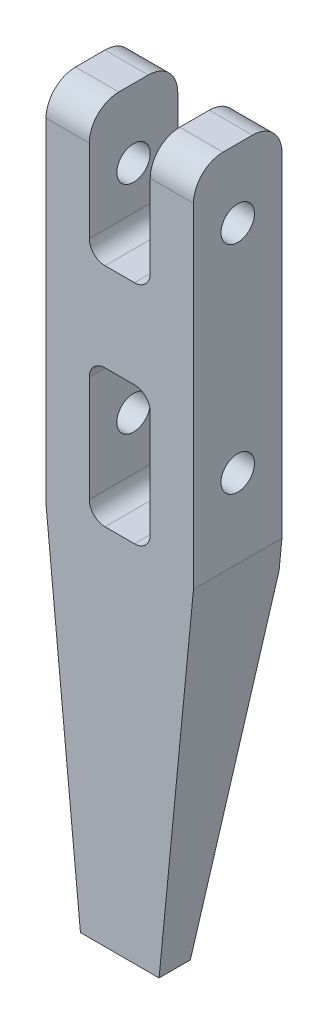
SolidWorks part; units mm, degrees
ref_plane "前视基准面" through (0, 0, 0) normal (0, 0, 1) x (1, 0, 0)
ref_plane "上视基准面" through (0, 0, 0) normal (0, 1, 0) x (1, 0, 0)
ref_plane "右视基准面" through (0, 0, 0) normal (1, 0, 0) x (0, 0, -1)
sketch "草图1" plane through (0, 0, 0) normal (1, 0, 0) x (0, 0, -1)
  line L0 (0, 0) -> (0, -11) construction
  line L1 (-2.25, 3.5) -> (2.25, 3.5)
  line L2 (2.25, 3.5) -> (2.25, -16.5)
  line L3 (2.25, -16.5) -> (-0.6594, -33)
  line L4 (-0.6594, -33) -> (-2.25, -33)
  line L5 (-2.25, -33) -> (-2.25, 3.5)
  circle A0 centre (0, 0) radius 0.85
  circle A1 centre (0, -11) radius 0.85
  dimension "D1" = 1.7
  dimension "D2" = 11
  dimension "D3" = 100
  dimension "D4" = 3.5
  dimension "D5" = 4.5
  dimension "D6" = 20
  dimension "D7" = 22
extrude "凸台-拉伸1" add sketch "草图1" along normal mid plane 7.5
sketch "草图2" plane through (0, 0, 0) normal (0, 0, 1) x (1, 0, 0)
  line L0 (3.75, -0.85) -> (3.75, 0.85) construction
  line L1 (3.75, -11.85) -> (3.75, -10.15) construction
  line L2 (3.75, -0.85) -> (3.75, 0.85)
  line L3 (3.75, -11.85) -> (3.75, -10.15)
  line L4 (0, 0) -> (0, -31.8275) construction
  line L5 (3.75, 0) -> (-9.2261, 0) construction
  line L6 (3.75, -11) -> (-10.1426, -11) construction
  line L8 (-1.55, 4.7829) -> (1.55, 4.7829)
  line L9 (-1.55, 4.7829) -> (-1.55, -3)
  line L10 (-1.55, -3) -> (1.55, -3)
  line L11 (1.55, 4.7829) -> (1.55, -3)
  line L12 (-1.55, -7.5) -> (1.55, -7.5)
  line L13 (-1.55, -7.5) -> (-1.55, -14.5)
  line L14 (-1.55, -14.5) -> (1.55, -14.5)
  line L15 (1.55, -7.5) -> (1.55, -14.5)
  dimension "D1" = 7
  dimension "D2" = 3.1
  dimension "D3" = 3
extrude "切除-拉伸1" cut sketch "草图2" against normal through all and the other way through all contours L11 L8 L9 L10 | L15 L14 L13 L12
fillet "圆角1" radius 1.5 4 edges at (2.65, 3.5, 2.25) (2.65, 3.5, -2.25) (-2.65, 3.5, -2.25) (-2.65, 3.5, 2.25)
fillet "圆角2" radius 0.8 6 edges at (1.55, -7.5, 0) (-1.55, -7.5, 0) (1.55, -14.5, 0) (-1.55, -14.5, 0) (-1.55, -3, 0) (1.55, -3, 0)
sketch "草图3" plane through (0, 0, 2.25) normal (0, 0, 1) x (1, 0, 0)
  line L0 (-3.75, -15) -> (-2, -33)
  line L1 (-3.75, 2) -> (-3.75, -33) construction
  line L2 (3.75, -33) -> (-3.75, -33) construction
  line L3 (-2, -33) -> (-6.8574, -33)
  line L4 (-6.8574, -33) -> (-3.75, -15)
  line L5 (0, 0) -> (0, -34.8825) construction
  line L6 (6.8574, -33) -> (3.75, -15)
  line L7 (2, -33) -> (6.8574, -33)
  line L8 (3.75, -15) -> (2, -33)
  dimension "D1" = 18
  dimension "D2" = 4
extrude "切除-拉伸2" cut sketch "草图3" against normal through all
